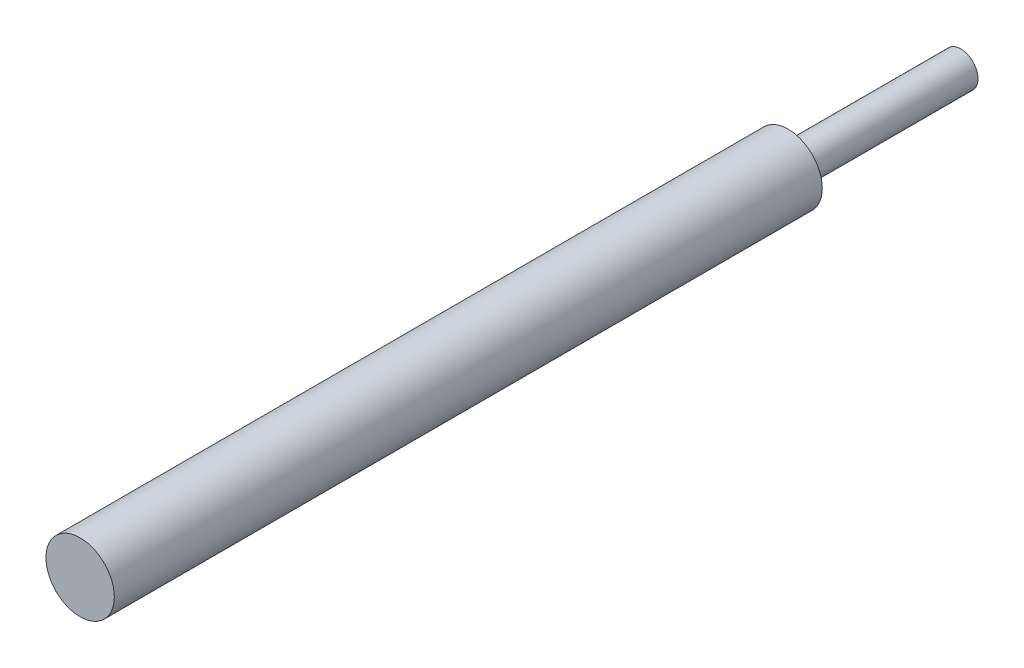
SolidWorks part; units mm, degrees
ref_plane "Ön Düzlem" through (0, 0, 0) normal (0, 0, 1) x (1, 0, 0)
ref_plane "Üst Düzlem" through (0, 0, 0) normal (0, 1, 0) x (1, 0, 0)
ref_plane "Sağ Düzlem" through (0, 0, 0) normal (1, 0, 0) x (0, 0, -1)
sketch "Çizim1" plane through (0, 0, 0) normal (0, 0, 1) x (1, 0, 0)
  circle A0 centre (0, 0) radius 9.9
extrude "Yükseklik-Ekstrüzyon1" add sketch "Çizim1" along normal blind 149 and the other way blind 106
ref_plane "Düzlem1" through (0, 0, -106) normal (0, 0, -1) x (-1, 0, 0)
ref_plane "Düzlem2" through (0, 0, -50.8425) normal (0, 0, -1) x (-1, 0, 0)
sketch "Çizim2" plane through (0, 0, -50.8425) normal (0, 0, -1) x (-1, 0, 0)
  circle A0 centre (0, 0) radius 9.9 construction
  circle A1 centre (0, 0) radius 9.9
ref_plane "Düzlem3" through (0, 0, 149) normal (0, 0, 1) x (1, 0, 0)
ref_plane "Düzlem4" through (0, 0, 94.0962) normal (0, 0, 1) x (1, 0, 0)
sketch "Çizim3" plane through (0, 0, 94.0962) normal (0, 0, 1) x (1, 0, 0)
  circle A0 centre (0, 0) radius 9.9 construction
  circle A1 centre (0, 0) radius 9.9
sketch "Çizim4" plane through (0, 0, -106) normal (0, 0, -1) x (-1, 0, 0)
  circle A0 centre (0, 0) radius 5
  circle A1 centre (0, 0) radius 9.9 construction
  circle A2 centre (0, 0) radius 9.9
extrude "Kes-Ekstrüzyon4" cut sketch "Çizim4" against normal blind 50 contours A0 | A2
